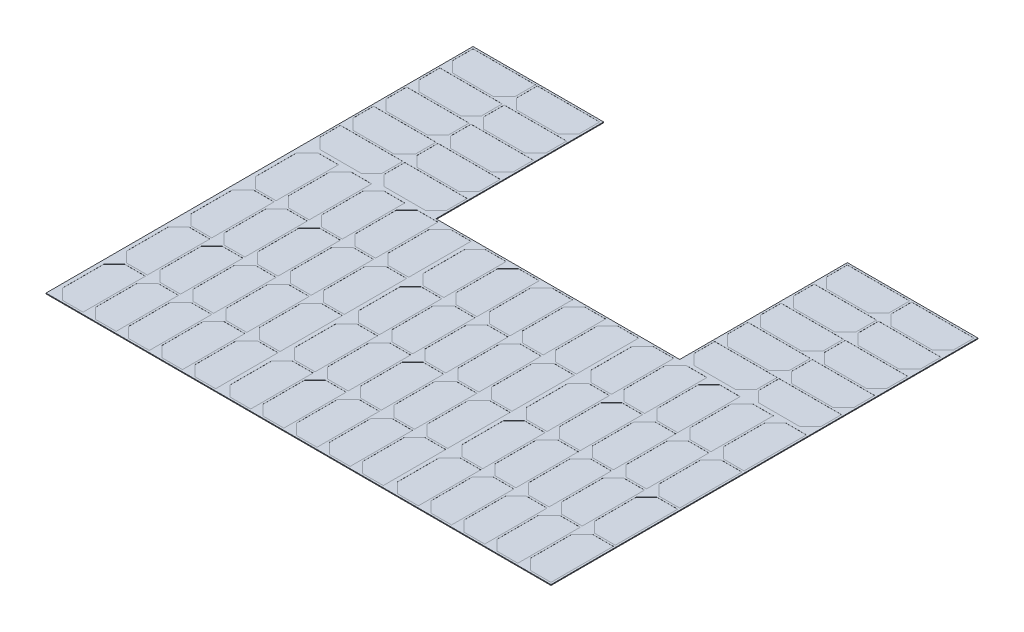
SolidWorks part; units mm, degrees
ref_plane "Front Plane" through (0, 0, 0) normal (0, 0, 1) x (1, 0, 0)
ref_plane "Top Plane" through (0, 0, 0) normal (0, 1, 0) x (1, 0, 0)
ref_plane "Right Plane" through (0, 0, 0) normal (1, 0, 0) x (0, 0, -1)
sketch "Sketch1" plane through (0, 0, 0) normal (0, 1, 0) x (1, 0, 0)
  line L0 (-107.0578, 273.2823) -> (-107.0578, 58.2823)
  line L1 (-274.5578, 273.2823) -> (-107.0578, 273.2823)
  line L2 (-274.5578, 273.2823) -> (-274.5578, -274.2177)
  line L3 (-274.5578, -274.2177) -> (372.9422, -274.2177)
  line L4 (372.9422, 273.2823) -> (372.9422, -274.2177)
  line L5 (-107.0578, 58.2823) -> (205.4422, 58.2823)
  line L6 (205.4422, 58.2823) -> (205.4422, 273.2823)
  line L7 (205.4422, 273.2823) -> (372.9422, 273.2823)
  dimension "D1" = 547.5
  dimension "D2" = 647.5
  dimension "D3" = 167.5
  dimension "D4" = 167.5
  dimension "D5" = 215
extrude "Boss-Extrude1" add sketch "Sketch1" along normal blind 1 contours L2 L3 L4 L7 L6 L5 L0 L1
sketch "Sketch2" plane through (0, 1, 0) normal (0, 1, 0) x (1, 0, 0)
  line L0 (-269.5578, -205.2177) -> (-269.5578, -258.2177)
  line L1 (-269.5578, -258.2177) -> (-256.0578, -271.7177)
  line L2 (-256.0578, -271.7177) -> (-229.5578, -271.7177)
  line L3 (-229.5578, -271.7177) -> (-229.5578, -191.7177)
  line L4 (-229.5578, -191.7177) -> (-256.0578, -191.7177)
  line L5 (-256.0578, -191.7177) -> (-269.5578, -205.2177)
  line L6 (-274.5578, 273.2823) -> (-274.5578, -274.2177) construction
  line L7 (-274.5578, -274.2177) -> (372.9422, -274.2177) construction
  dimension "D1" = 5
  dimension "D2" = 40
  dimension "D3" = 80
  dimension "D4" = 13.5
  dimension "D5" = 2.5
  dimension "D6" = 13.5
  dimension "D7" = 13.5
  dimension "D8" = 13.5
extrude "Cut-Extrude1" cut sketch "Sketch2" against normal blind 0.11
pattern_linear "LPattern1" count 5 spacing 42.5 along (1, 0, 0) count 4 spacing 82.5 along (0, 0, -1) of "Cut-Extrude1"
pattern_linear "LPattern2" count 3 spacing 215 along (1, 0, 0) of "LPattern1", "Cut-Extrude1"
sketch "Sketch3" plane through (0, 1, 0) normal (0, 1, 0) x (1, 0, 0)
  line L8 (-272.0578, 74.2823) -> (-272.0578, 100.7823)
  line L9 (-272.0578, 100.7823) -> (-192.0578, 100.7823)
  line L10 (-192.0578, 100.7823) -> (-192.0578, 74.2823)
  line L11 (-192.0578, 74.2823) -> (-205.5578, 60.7823)
  line L12 (-205.5578, 60.7823) -> (-258.5578, 60.7823)
  line L13 (-258.5578, 60.7823) -> (-272.0578, 74.2823)
  line L14 (-229.5578, 55.7823) -> (-256.0578, 55.7823) construction
  line L15 (-274.5578, 273.2823) -> (-274.5578, -274.2177) construction
  point P15 (-232.0578, 60.7823)
  point P16 (-232.0578, 100.7823)
  dimension "D6" = 80
  dimension "D7" = 40
  dimension "D8" = 13.5
  dimension "D9" = 13.5
  dimension "D10" = 5
  dimension "D11" = 2.5
extrude "Cut-Extrude2" cut sketch "Sketch3" against normal blind 0.11
pattern_linear "LPattern3" count 5 spacing 42.5 along (0, 0, -1) count 2 spacing 82.5 along (1, 0, 0) of "Cut-Extrude2"
pattern_linear "LPattern4" count 2 spacing 480 along (1, 0, 0) of "LPattern3", "Cut-Extrude2"
sketch "Sketch4" plane through (0, 1, 0) normal (0, 1, 0) x (1, 0, 0)
  line L0 (-229.5578, -191.7177) -> (-256.0578, -191.7177) construction
  line L1 (-270.8078, -190.4677) -> (-58.3078, -190.4677)
  line L2 (-270.8078, -190.4677) -> (-270.8078, -272.9677)
  line L3 (-270.8078, -272.9677) -> (-58.3078, -272.9677)
  line L4 (-58.3078, -190.4677) -> (-58.3078, -272.9677)
  line L5 (-274.5578, -274.2177) -> (372.9422, -274.2177) construction
  line L6 (-269.5578, -205.2177) -> (-269.5578, -258.2177) construction
  line L7 (-59.5578, -271.7177) -> (-59.5578, -191.7177) construction
  line L8 (-270.8078, -107.9677) -> (-58.3078, -107.9677)
  line L9 (-270.8078, -107.9677) -> (-270.8078, -190.4677)
  line L10 (-58.3078, -107.9677) -> (-58.3078, -190.4677)
  line L11 (-270.8078, -25.4677) -> (-58.3078, -25.4677)
  line L12 (-270.8078, -25.4677) -> (-270.8078, -107.9677)
  line L13 (-58.3078, -25.4677) -> (-58.3078, -107.9677)
  line L14 (-270.8078, 57.0323) -> (-58.3078, 57.0323)
  line L15 (-270.8078, 57.0323) -> (-270.8078, -25.4677)
  line L16 (-58.3078, 57.0323) -> (-58.3078, -25.4677)
  line L17 (-55.8078, 57.0323) -> (156.6922, 57.0323)
  line L18 (156.6922, 57.0323) -> (156.6922, -25.4677)
  line L19 (-55.8078, -25.4677) -> (156.6922, -25.4677)
  line L20 (156.6922, -25.4677) -> (156.6922, -107.9677)
  line L21 (-55.8078, -107.9677) -> (156.6922, -107.9677)
  line L22 (-55.8078, -190.4677) -> (156.6922, -190.4677)
  line L23 (156.6922, -107.9677) -> (156.6922, -190.4677)
  line L24 (156.6922, -190.4677) -> (156.6922, -272.9677)
  line L25 (-55.8078, -272.9677) -> (156.6922, -272.9677)
  line L26 (-55.8078, 57.0323) -> (-55.8078, -25.4677)
  line L27 (-55.8078, -25.4677) -> (-55.8078, -107.9677)
  line L28 (-55.8078, -107.9677) -> (-55.8078, -190.4677)
  line L29 (-55.8078, -190.4677) -> (-55.8078, -272.9677)
  line L30 (159.1922, 57.0323) -> (371.6922, 57.0323)
  line L31 (371.6922, 57.0323) -> (371.6922, -25.4677)
  line L32 (159.1922, -25.4677) -> (371.6922, -25.4677)
  line L33 (371.6922, -25.4677) -> (371.6922, -107.9677)
  line L34 (159.1922, -107.9677) -> (371.6922, -107.9677)
  line L35 (159.1922, -190.4677) -> (371.6922, -190.4677)
  line L36 (371.6922, -107.9677) -> (371.6922, -190.4677)
  line L37 (371.6922, -190.4677) -> (371.6922, -272.9677)
  line L38 (159.1922, -272.9677) -> (371.6922, -272.9677)
  line L39 (159.1922, 57.0323) -> (159.1922, -25.4677)
  line L40 (159.1922, -25.4677) -> (159.1922, -107.9677)
  line L41 (159.1922, -107.9677) -> (159.1922, -190.4677)
  line L42 (159.1922, -190.4677) -> (159.1922, -272.9677)
  line L43 (-258.5578, 60.7823) -> (-205.5578, 60.7823) construction
  line L44 (-273.3078, 272.0323) -> (-190.8078, 272.0323)
  line L45 (-273.3078, 272.0323) -> (-273.3078, 59.5323)
  line L46 (-273.3078, 59.5323) -> (-190.8078, 59.5323)
  line L47 (-190.8078, 272.0323) -> (-190.8078, 59.5323)
  line L48 (-272.0578, 100.7823) -> (-272.0578, 74.2823) construction
  line L49 (-192.0578, 74.2823) -> (-192.0578, 100.7823) construction
  line L51 (-192.0578, 270.7823) -> (-272.0578, 270.7823) construction
  line L52 (-190.8078, 272.0323) -> (-108.3078, 272.0323)
  line L53 (-108.3078, 272.0323) -> (-108.3078, 59.5323)
  line L54 (-190.8078, 59.5323) -> (-108.3078, 59.5323)
  line L55 (206.6922, 272.0323) -> (289.1922, 272.0323)
  line L56 (206.6922, 272.0323) -> (206.6922, 59.5323)
  line L57 (206.6922, 59.5323) -> (289.1922, 59.5323)
  line L58 (289.1922, 272.0323) -> (289.1922, 59.5323)
  line L59 (289.1922, 272.0323) -> (371.6922, 272.0323)
  line L60 (371.6922, 272.0323) -> (371.6922, 59.5323)
  line L61 (289.1922, 59.5323) -> (371.6922, 59.5323)
  dimension "D1" = 1.25
  dimension "D2" = 1.25
  dimension "2.5/2" = 1.25
  dimension "D3" = 1.25
  dimension "D5" = 82.5
  dimension "D6" = 3
  dimension "D7" = 2.5
  dimension "D8" = 1.25
  dimension "D9" = 1.25
  dimension "D10" = 1.25
  dimension "D11" = 1.25
  dimension "D13" = 82.5
  dimension "D4" = 4
  dimension "D12" = 2
  dimension "D14" = 2
